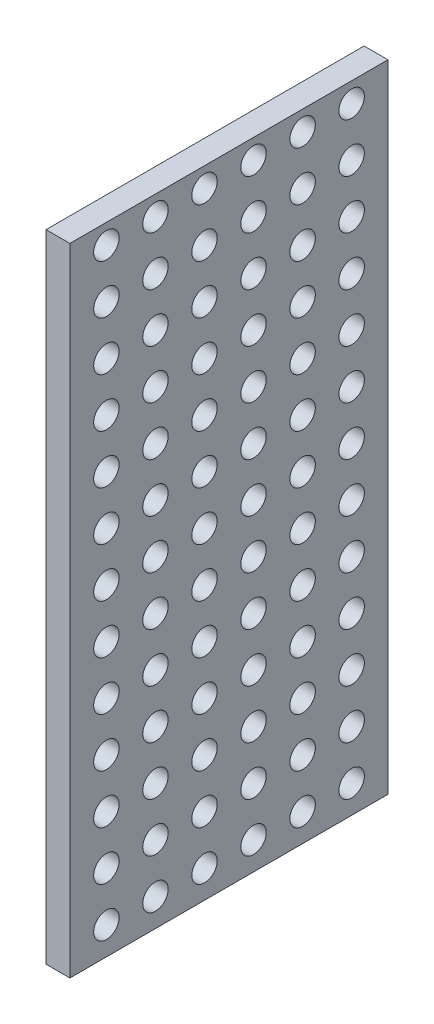
SolidWorks part; units mm, degrees
ref_plane "Front Plane" through (0, 0, 0) normal (0, 0, 1) x (1, 0, 0)
ref_plane "Top Plane" through (0, 0, 0) normal (0, 1, 0) x (1, 0, 0)
ref_plane "Right Plane" through (0, 0, 0) normal (1, 0, 0) x (0, 0, -1)
sketch "Sketch1" plane through (0, 0, 0) normal (1, 0, 0) x (0, 0, -1)
  line L1 (-25, -50) -> (25, -50)
  line L2 (-25, -50) -> (-25, 50)
  line L3 (-25, 50) -> (25, 50)
  line L4 (25, -50) -> (25, 50)
  line L5 (-25, -50) -> (25, 50) construction
  line L6 (-25, 50) -> (25, -50) construction
  point P0 (0, 0)
  dimension "D1" = 50
  dimension "D2" = 100
extrude "Boss-Extrude1" add sketch "Sketch1" along normal blind 3.75
sketch "Sketch2" plane through (0, 0, 0) normal (-1, 0, 0) x (0, 0, 1)
  line L0 (-25, 50) -> (25, 50) construction
  line L1 (-19.29, 46.895) -> (-11.58, 46.895) construction
  line L2 (-25, -50) -> (-25, 50) construction
  circle A0 centre (-19.29, 46.895) radius 2
  circle A9 centre (-11.58, 46.895) radius 2
  circle A10 centre (-3.87, 46.895) radius 2
  circle A11 centre (3.84, 46.895) radius 2
  circle A12 centre (11.55, 46.895) radius 2
  circle A13 centre (19.26, 46.895) radius 2
  circle A14 centre (-19.29, 39.185) radius 2
  circle A15 centre (-11.58, 39.185) radius 2
  circle A16 centre (-3.87, 39.185) radius 2
  circle A17 centre (3.84, 39.185) radius 2
  circle A18 centre (11.55, 39.185) radius 2
  circle A19 centre (19.26, 39.185) radius 2
  circle A20 centre (-19.29, 31.475) radius 2
  circle A21 centre (-11.58, 31.475) radius 2
  circle A22 centre (-3.87, 31.475) radius 2
  circle A23 centre (3.84, 31.475) radius 2
  circle A24 centre (11.55, 31.475) radius 2
  circle A25 centre (19.26, 31.475) radius 2
  circle A26 centre (-19.29, 23.765) radius 2
  circle A27 centre (-11.58, 23.765) radius 2
  circle A28 centre (-3.87, 23.765) radius 2
  circle A29 centre (3.84, 23.765) radius 2
  circle A30 centre (11.55, 23.765) radius 2
  circle A31 centre (19.26, 23.765) radius 2
  circle A32 centre (-19.29, 16.055) radius 2
  circle A33 centre (-11.58, 16.055) radius 2
  circle A34 centre (-3.87, 16.055) radius 2
  circle A35 centre (3.84, 16.055) radius 2
  circle A36 centre (11.55, 16.055) radius 2
  circle A37 centre (19.26, 16.055) radius 2
  circle A38 centre (-19.29, 8.345) radius 2
  circle A39 centre (-11.58, 8.345) radius 2
  circle A40 centre (-3.87, 8.345) radius 2
  circle A41 centre (3.84, 8.345) radius 2
  circle A42 centre (11.55, 8.345) radius 2
  circle A43 centre (19.26, 8.345) radius 2
  circle A44 centre (-19.29, 0.635) radius 2
  circle A45 centre (-11.58, 0.635) radius 2
  circle A46 centre (-3.87, 0.635) radius 2
  circle A47 centre (3.84, 0.635) radius 2
  circle A48 centre (11.55, 0.635) radius 2
  circle A49 centre (19.26, 0.635) radius 2
  circle A50 centre (-19.29, -7.075) radius 2
  circle A51 centre (-11.58, -7.075) radius 2
  circle A52 centre (-3.87, -7.075) radius 2
  circle A53 centre (3.84, -7.075) radius 2
  circle A54 centre (11.55, -7.075) radius 2
  circle A55 centre (19.26, -7.075) radius 2
  circle A56 centre (-19.29, -14.785) radius 2
  circle A57 centre (-11.58, -14.785) radius 2
  circle A58 centre (-3.87, -14.785) radius 2
  circle A59 centre (3.84, -14.785) radius 2
  circle A60 centre (11.55, -14.785) radius 2
  circle A61 centre (19.26, -14.785) radius 2
  circle A62 centre (-19.29, -22.495) radius 2
  circle A63 centre (-11.58, -22.495) radius 2
  circle A64 centre (-3.87, -22.495) radius 2
  circle A65 centre (3.84, -22.495) radius 2
  circle A66 centre (11.55, -22.495) radius 2
  circle A67 centre (19.26, -22.495) radius 2
  circle A68 centre (-19.29, -30.205) radius 2
  circle A69 centre (-11.58, -30.205) radius 2
  circle A70 centre (-3.87, -30.205) radius 2
  circle A71 centre (3.84, -30.205) radius 2
  circle A72 centre (11.55, -30.205) radius 2
  circle A73 centre (19.26, -30.205) radius 2
  circle A74 centre (-19.29, -37.915) radius 2
  circle A75 centre (-11.58, -37.915) radius 2
  circle A76 centre (-3.87, -37.915) radius 2
  circle A77 centre (3.84, -37.915) radius 2
  circle A78 centre (11.55, -37.915) radius 2
  circle A79 centre (19.26, -37.915) radius 2
  circle A80 centre (-19.29, -45.625) radius 2
  circle A81 centre (-11.58, -45.625) radius 2
  circle A82 centre (-3.87, -45.625) radius 2
  circle A83 centre (3.84, -45.625) radius 2
  circle A84 centre (11.55, -45.625) radius 2
  circle A85 centre (19.26, -45.625) radius 2
  dimension "D2" = 4
  dimension "D3" = 6
  dimension "D7" = 7.71
  dimension "D1" = 3.105
  dimension "D4" = 7.71
  dimension "D5" = 5.71
  dimension "D6" = 8
  dimension "D8" = 6
extrude "Cut-Extrude1" cut sketch "Sketch2" against normal blind 3.75
sketch "Sketch5" plane through (0, 0, -25) normal (0, 0, -1) x (-1, 0, 0)
  line L0 (-3.75, -50) -> (-3.75, 50) construction
  line L1 (-3.75, -50) -> (0, -50) construction
  circle A0 centre (-1.875, 4) radius 1.2
  circle A1 centre (-1.875, -45) radius 1.2
  dimension "D2" = 2.4
  dimension "D3" = 2.4
  dimension "D1" = 49
  dimension "D4" = 1.875
  dimension "D5" = 1.875
  dimension "D6" = 5
extrude "Cut-Extrude2" cut sketch "Sketch5" against normal blind 1.875 contours A1 | A0
